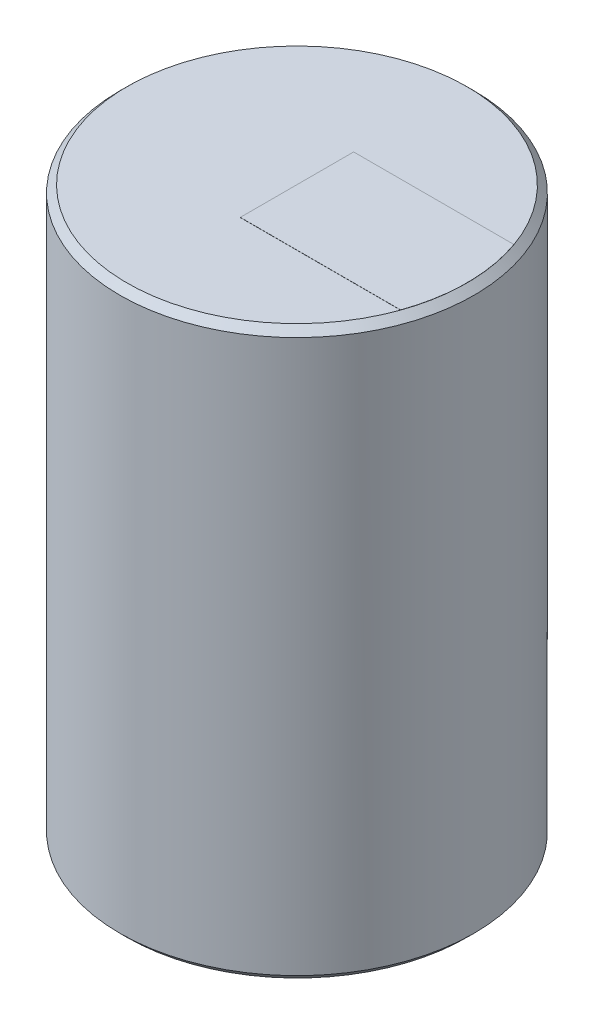
SolidWorks part; units mm, degrees
material "PE High Density"
ref_plane "Front Plane" through (0, 0, 0) normal (0, 0, 1) x (1, 0, 0)
ref_plane "Top Plane" through (0, 0, 0) normal (0, 1, 0) x (1, 0, 0)
ref_plane "Right Plane" through (0, 0, 0) normal (1, 0, 0) x (0, 0, -1)
sketch "Sketch1" plane through (0, 0, 0) normal (0, 1, 0) x (1, 0, 0)
  circle A0 centre (0, 0) radius 12.5
  dimension "D1" = 25
extrude "Boss-Extrude1" add sketch "Sketch1" along normal blind 40
chamfer "Chamfer1" distance 0.5 angle 45 2 edges at (0, 0, 12.5) (0, 40, 12.5)
sketch "Sketch2" plane through (0, 40, 0) normal (0, 1, 0) x (1, 0, 0)
  line L0 (0, -1000) -> (0, 49000) construction
  line L1 (-1000, 0) -> (49000, 0) construction
  line L2 (11.3137, 4) -> (0, 4)
  line L3 (11.3137, -4) -> (0, -4)
  line L4 (0, 4) -> (0, -4)
  circle A0 centre (0, 0) radius 12 construction
  arc A1 (11.3137, -4) -> (11.3137, 4) centre (0, 0) ccw
  dimension "D1" = 8
extrude "Boss-Extrude2" add sketch "Sketch2" along normal blind 0.01
